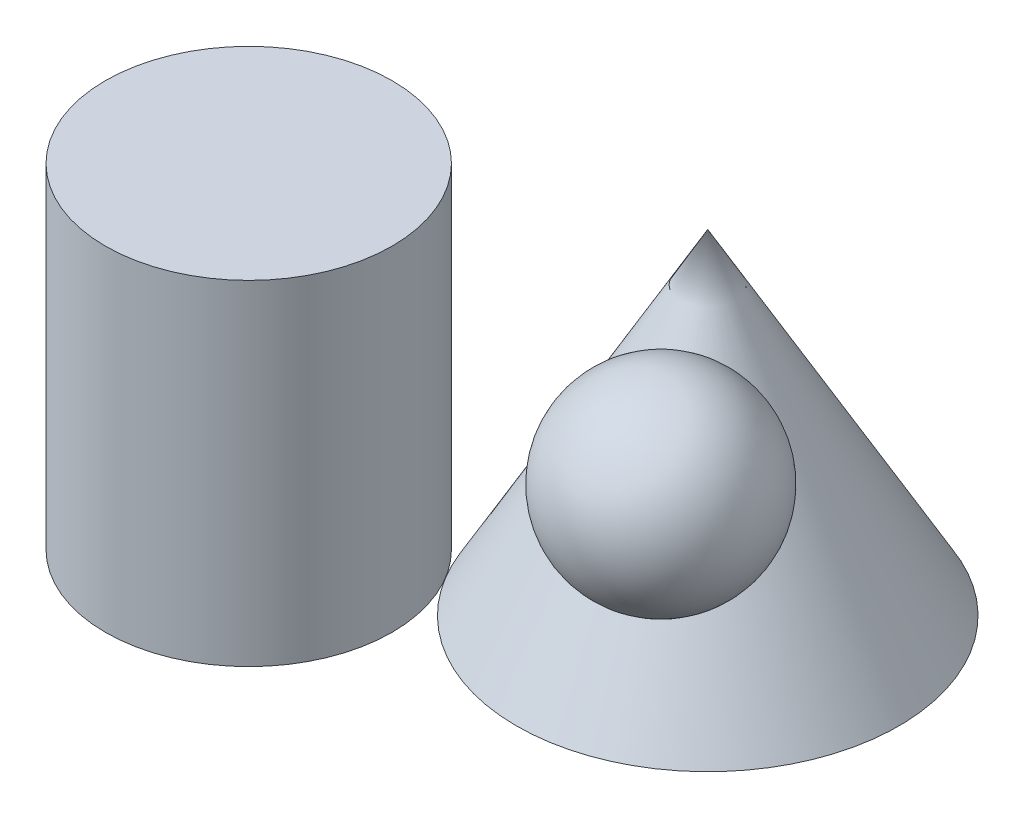
SolidWorks part; units mm, degrees
ref_plane "Front Plane" through (0, 0, 0) normal (0, 0, 1) x (1, 0, 0)
ref_plane "Top Plane" through (0, 0, 0) normal (0, 1, 0) x (1, 0, 0)
ref_plane "Right Plane" through (0, 0, 0) normal (1, 0, 0) x (0, 0, -1)
sketch "Sketch1" plane through (0, 0, 0) normal (0, 1, 0) x (1, 0, 0)
  circle A0 centre (0, 0) radius 40 construction
  circle A1 centre (-60, -36.0555) radius 30
  dimension "D1" = 80
  dimension "D2" = 60
  dimension "D3" = 60
sketch "Sketch2" plane through (0, 0, 0) normal (0, 0, 1) x (1, 0, 0)
  line L0 (0, 0) -> (0, 70)
  line L1 (40, 0) -> (-40, 0) construction
  line L2 (0, 70) -> (40, 0)
  line L3 (40, 0) -> (0, 0)
  dimension "D1" = 40
  dimension "D2" = 70
revolve "Revolve1" add sketch "Sketch2" angle 360 about L0
extrude "Extrude1" add sketch "Sketch1" along normal blind 70
sketch "Sketch4" plane through (0, 0, 0) normal (0, 1, 0) x (1, 0, 0)
  line L0 (40, 0) -> (0, 0) construction
  line L1 (0, 0) -> (0, -40) construction
  line L2 (10, 0) -> (10, -40)
  line L3 (40, -15) -> (0, -15)
  line L4 (0, 0) -> (10, -15)
  circle A0 centre (0, 0) radius 40 construction
  dimension "D1" = 10
  dimension "D2" = 15
ref_plane "Plane1" through (0, 0, 0) normal (-0.8321, 0, 0.5547) x (0.5547, 0, 0.8321)
sketch "Sketch6" plane through (0, 0, 0) normal (-0.8321, 0, 0.5547) x (0.5547, 0, 0.8321)
  line L0 (18.0278, 0) -> (18.0278, 38.4514) construction
  line L1 (0, 70) -> (40, 0) construction
  line L2 (18.0278, 38.4514) -> (35.3926, 48.3742) construction
  line L3 (35.3926, 68.3742) -> (35.3926, 28.3742)
  arc A0 (35.3926, 68.3742) -> (35.3926, 28.3742) centre (35.3926, 48.3742) ccw
  dimension "D1" = 20
revolve "Revolve2" add sketch "Sketch6" angle 360 about L3
